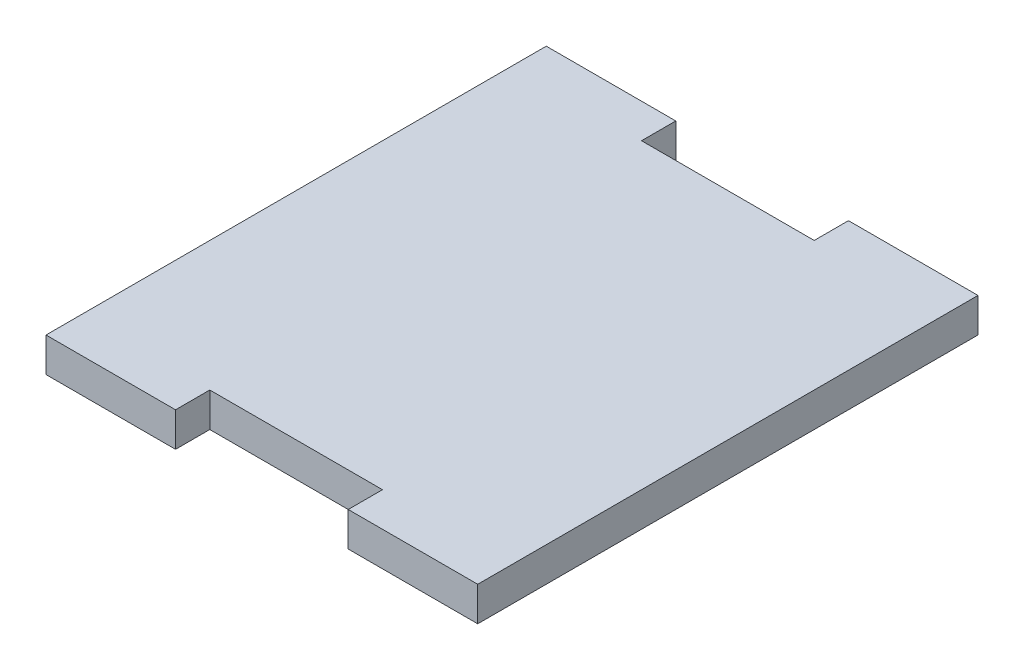
SolidWorks part; units mm, degrees
ref_plane "Front Plane" through (0, 0, 0) normal (0, 0, 1) x (1, 0, 0)
ref_plane "Top Plane" through (0, 0, 0) normal (0, 1, 0) x (1, 0, 0)
ref_plane "Right Plane" through (0, 0, 0) normal (1, 0, 0) x (0, 0, -1)
sketch "Sketch1" plane through (0, 0, 0) normal (0, 1, 0) x (1, 0, 0)
  line L1 (-25.5302, -14.8529) -> (-13.5302, -14.8529)
  line L2 (-13.5302, -14.8529) -> (-13.5302, -11.6779)
  line L3 (-13.5302, -11.6779) -> (2.4698, -11.6779)
  line L4 (2.4698, -11.6779) -> (2.4698, -14.8529)
  line L5 (2.4698, -14.8529) -> (14.4698, -14.8529)
  line L6 (14.4698, -14.8529) -> (14.4698, 31.4971)
  line L7 (14.4698, 31.4971) -> (2.4698, 31.4971)
  line L8 (2.4698, 31.4971) -> (2.4698, 28.3221)
  line L9 (2.4698, 28.3221) -> (-13.5302, 28.3221)
  line L10 (-13.5302, 28.3221) -> (-13.5302, 31.4971)
  line L11 (-13.5302, 31.4971) -> (-25.5302, 31.4971)
  line L13 (-25.5302, 31.4971) -> (-25.5302, -14.8529)
  dimension "D1" = 16
  dimension "D2" = 12
  dimension "D3" = 3.175
  dimension "D4" = 40
extrude "Boss-Extrude1" add sketch "Sketch1" along normal blind 3.175
